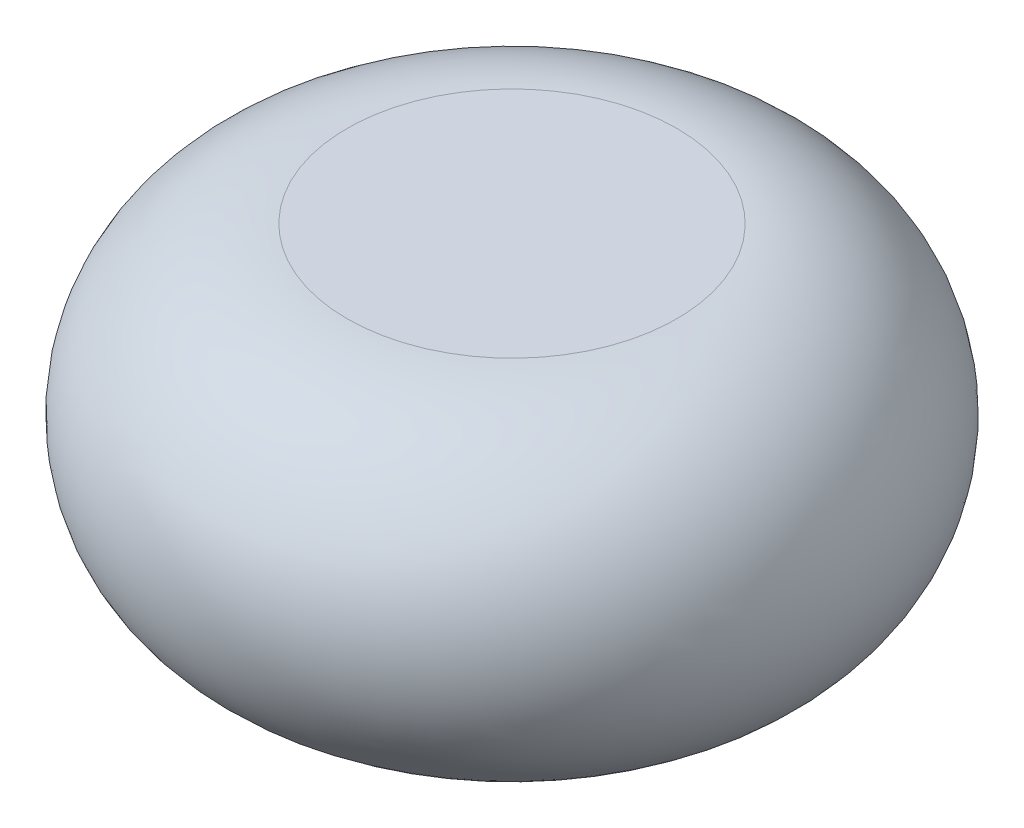
SolidWorks part; units mm, degrees
ref_plane "Front Plane" through (0, 0, 0) normal (0, 0, 1) x (1, 0, 0)
ref_plane "Top Plane" through (0, 0, 0) normal (0, 1, 0) x (1, 0, 0)
ref_plane "Right Plane" through (0, 0, 0) normal (1, 0, 0) x (0, 0, -1)
sketch "Sketch1" plane through (0, 0, 0) normal (0, 0, 1) x (1, 0, 0)
  line L0 (0, 500) -> (0, -500)
  line L1 (0, -500) -> (500, -500)
  line L3 (0, 500) -> (500, 500)
  arc A0 (500, -500) -> (500, 500) centre (500, 0) ccw
  point P0 (0, 0)
  dimension "D1" = 500
  dimension "D2" = 1000
  dimension "D3" = 500
ref_axis "Axis1" through (0, 550, 0) along (0, -1, 0)
revolve "Revolve2" add sketch "Sketch1" angle 360 about axis through (0, 550, 0) along (0, -1, 0)
